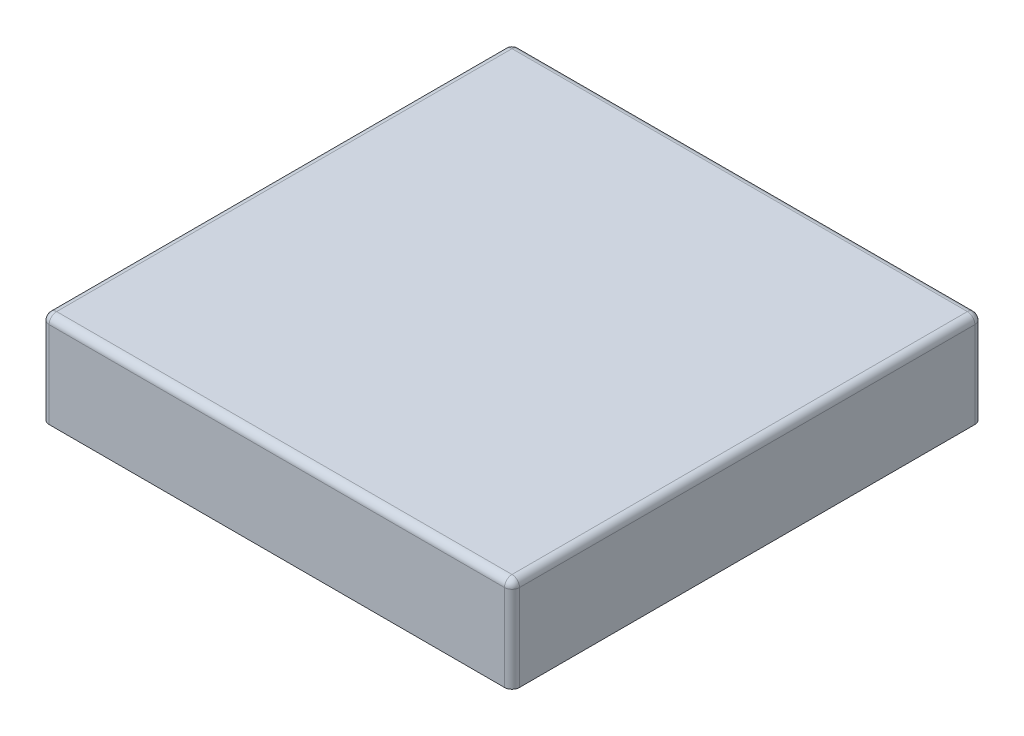
SolidWorks part; units mm, degrees
ref_plane "Front Plane" through (0, 0, 0) normal (0, 0, 1) x (1, 0, 0)
ref_plane "Top Plane" through (0, 0, 0) normal (0, 1, 0) x (1, 0, 0)
ref_plane "Right Plane" through (0, 0, 0) normal (1, 0, 0) x (0, 0, -1)
sketch "Sketch2" plane through (0, 0, 0) normal (0, 1, 0) x (1, 0, 0)
  line L0 (-17.7331, 8.7234) -> (-1.8581, 8.7234)
  line L1 (-1.8581, 8.7234) -> (-1.8581, -7.1516)
  line L2 (-1.8581, -7.1516) -> (-17.7331, -7.1516)
  line L3 (-17.7331, -7.1516) -> (-17.7331, 8.7234)
  dimension "D1" = 15.875
  dimension "D2" = 15.875
extrude "Boss-Extrude3" add sketch "Sketch2" along normal blind 3.175
shell "Shell1" thickness 1.524
sketch "Sketch5" plane through (0, 0, 0) normal (0, -1, 0) x (1, 0, 0)
  circle A2 centre (-9.7956, -0.7859) radius 3.175
  circle A3 centre (-9.7956, -0.7859) radius 2.3876
  dimension "D1" = 6.35
  dimension "D2" = 4.7752
extrude "Boss-Extrude6" add sketch "Sketch5" against normal up to surface (1.651 mm away) up to face at (-9.7956, 1.651, -0.7859)
fillet "Fillet1" radius 0.254 8 edges at (-17.7331, 1.5875, -8.7234) (-1.8581, 1.5875, -8.7234) (-1.8581, 1.5875, 7.1516) (-1.8581, 3.175, -0.7859) (-9.7956, 3.175, -8.7234) (-17.7331, 3.175, -0.7859) (-17.7331, 1.5875, 7.1516) (-9.7956, 3.175, 7.1516)
